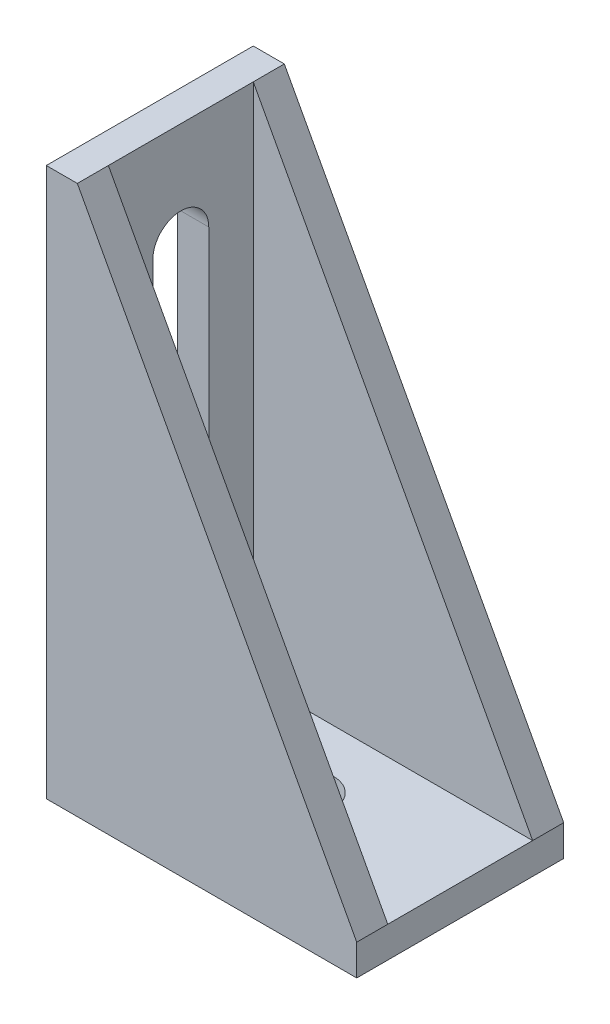
SolidWorks part; units mm, degrees
ref_plane "Front Plane" through (0, 0, 0) normal (0, 0, 1) x (1, 0, 0)
ref_plane "Top Plane" through (0, 0, 0) normal (0, 1, 0) x (1, 0, 0)
ref_plane "Right Plane" through (0, 0, 0) normal (1, 0, 0) x (0, 0, -1)
sketch "Sketch1" plane through (0, 0, 0) normal (0, 1, 0) x (1, 0, 0)
  line L1 (-15, 10) -> (15, 10)
  line L2 (-15, 10) -> (-15, -10)
  line L3 (-15, -10) -> (15, -10)
  line L4 (15, 10) -> (15, -10)
  line L5 (-15, 10) -> (15, -10) construction
  line L6 (-15, -10) -> (15, 10) construction
  circle A0 centre (0, 0) radius 2.75
  point P0 (0, 0)
  dimension "D3" = 5.5
  dimension "D1" = 30
  dimension "D2" = 20
extrude "Boss-Extrude1" add sketch "Sketch1" along normal blind 3
sketch "Sketch2" plane through (0, 3, 0) normal (0, 1, 0) x (1, 0, 0)
  line L0 (-15, -10) -> (15, -10) construction
  line L1 (-15, 10) -> (-12, 10)
  line L2 (-15, 10) -> (-15, -10)
  line L3 (-15, -10) -> (-12, -10)
  line L4 (-12, 10) -> (-12, -10)
  dimension "D1" = 3
extrude "Boss-Extrude2" add sketch "Sketch2" along normal blind 50
sketch "Sketch3" plane through (0, 0, 10) normal (0, 0, 1) x (1, 0, 0)
  line L0 (-12, 53) -> (15, 3)
rib "Rib1" sketch "Sketch3" sketch "Sketch3" thickness 3 extrusion direction parallel to sketch draft on no parameters "D1"=3
mirror "Mirror1" about plane through (0, 0, 0) normal (0, 0, 1) of "Rib1"
sketch "Sketch4" plane through (-12, 0, 0) normal (1, 0, 0) x (0, 0, -1)
  line L0 (0, 53) -> (0, 3) construction
  line L1 (-7, 53) -> (7, 53) construction
  line L2 (-7, 3) -> (7, 3) construction
  line L3 (0, 43) -> (0, 8) construction
  line L4 (2.7, 43) -> (2.7, 8)
  line L5 (-2.7, 43) -> (-2.7, 8)
  arc A0 (2.7, 43) -> (-2.7, 43) centre (0, 43) ccw
  arc A1 (-2.7, 8) -> (2.7, 8) centre (0, 8) ccw
  point P8 (0, 25.5)
  dimension "D1" = 2.7
  dimension "D2" = 10
  dimension "D3" = 5
extrude "Cut-Extrude1" cut sketch "Sketch4" against normal through all
